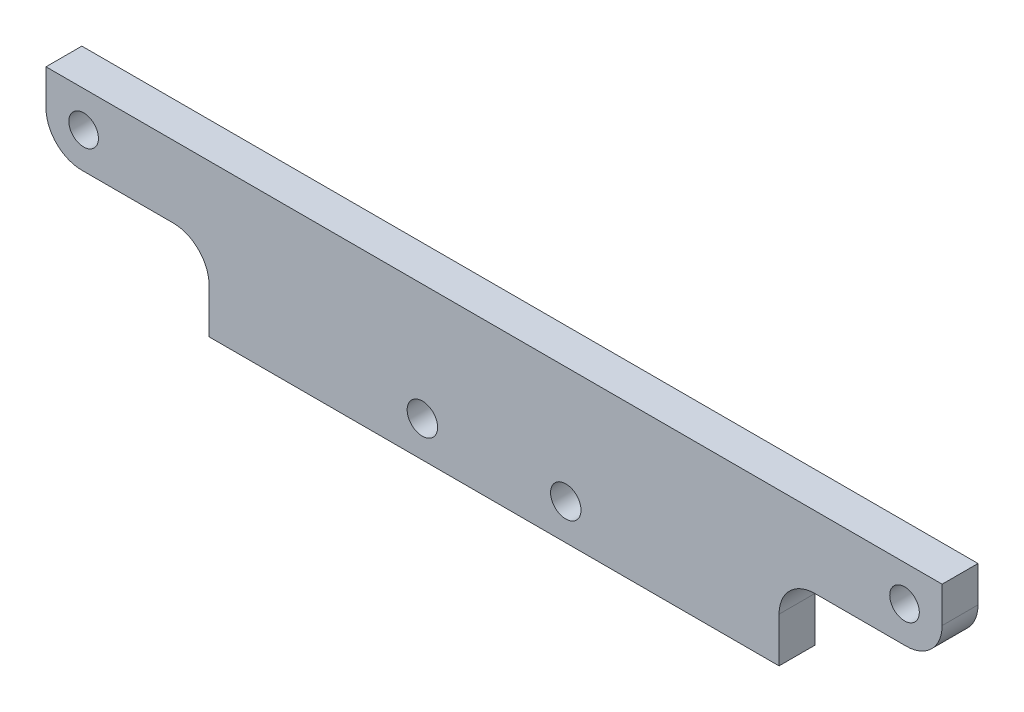
SolidWorks part; units mm, degrees
material "6061 Alloy"
ref_plane "Front Plane" through (0, 0, 0) normal (0, 0, 1) x (1, 0, 0)
ref_plane "Top Plane" through (0, 0, 0) normal (0, 1, 0) x (1, 0, 0)
ref_plane "Right Plane" through (0, 0, 0) normal (1, 0, 0) x (0, 0, -1)
sketch "Sketch2" plane through (0, 0, 0) normal (0, 0, 1) x (1, 0, 0)
  line L0 (50, 0) -> (-50, 0)
  line L1 (-50, 0) -> (-50, 17)
  line L2 (-50, 17) -> (50, 17)
  line L3 (50, 17) -> (50, 0)
  point P6 (0, 0)
  dimension "D1" = 17
  dimension "D2" = 100
extrude "Base" add sketch "Sketch2" along normal mid plane 4
hole_wizard "M3 Clearance Hole1" positions "Sketch5" profile "Sketch6" hole size "M3" standard "ANSI Metric" end condition through all
sketch "Sketch5" plane through (0, 4, -2) normal (0, 0, 1) x (1, 0, 0)
  line L4 (-50, -4) -> (50, -4) construction
  point P0 (-8, 0)
  point P2 (8, 0)
  point P38 (0, -4)
  dimension "D1" = 16
  dimension "D2" = 4
  dimension "D3" = 8
sketch "Sketch6" plane through (-8, 4, -2) normal (1, 0, 0) x (0, 1, 0)
  line L0 (0, 0) -> (0, 4)
  line L1 (0, 4) -> (1.7, 4)
  line L2 (1.7, 4) -> (1.7, 0)
  line L5 (1.7, 0) -> (0, 0)
  line L11 (0, -6.35) -> (0, 107.95) construction
  dimension "Thru Hole Dia." = 3.4
  dimension "Thru Hole Depth" = 4
hole_wizard "M4x0.7 Tapped Hole1" positions "Sketch7" profile "Sketch8" tap size "M4x0.7" standard "ANSI Metric" end condition through all
sketch "Sketch7" plane through (0, 0, -2) normal (0, 0, -1) x (-1, 0, 0)
  line L4 (-50, 17) -> (50, 17) construction
  point P0 (-45.8, 13)
  point P2 (45.8, 13)
  dimension "D1" = 91.6
  dimension "D2" = 45.8
  dimension "D3" = 4
sketch "Sketch8" plane through (45.8, 13, -2) normal (1, 0, 0) x (0, 1, 0)
  line L0 (0, 0) -> (0, 4)
  line L1 (0, 4) -> (1.65, 4)
  line L2 (1.65, 4) -> (1.65, 0)
  line L5 (1.65, 0) -> (0, 0)
  line L11 (0, -6.35) -> (0, 107.95) construction
  dimension "Thread Major Dia." = 3.3
  dimension "Thru Tap Drill Depth" = 4
sketch "Sketch9" plane through (0, 0, -2) normal (0, 0, -1) x (-1, 0, 0)
  line L0 (-31.8, 0) -> (-31.8, 9)
  line L1 (50, 0) -> (-50, 0) construction
  line L2 (-31.8, 9) -> (-50, 9)
  line L4 (31.8, 0) -> (31.8, 9)
  line L5 (31.8, 9) -> (50, 9)
  line L6 (50, 17) -> (50, 0) construction
  line L7 (50, 9) -> (50, 0)
  line L8 (50, 0) -> (31.8, 0)
  line L9 (-31.8, 0) -> (-50, 0)
  line L10 (-50, 0) -> (-50, 9)
  line L11 (-50, 0) -> (-50, 17) construction
  line L12 (-50, 17) -> (50, 17) construction
  line M9 (50, 0) -> (50, 17)
  line M12 (-50, 0) -> (50, 0)
  dimension "D1" = 8
  dimension "D2" = 18.2
  dimension "D3" = 18.2
extrude "Cut-Extrude1" cut sketch "Sketch9" against normal blind 10 contours L5 L4 M12 M9 | L2 L10 L9 L0
fillet "Fillet3" radius 4 4 edges at (-50, 9, 0) (-31.8, 9, 0) (50, 9, 0) (31.8, 9, 0)
